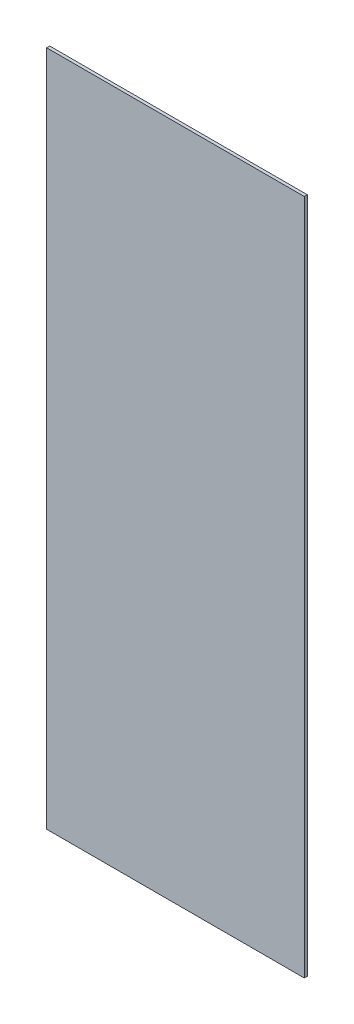
SolidWorks part; units mm, degrees
ref_plane "Front Plane" through (0, 0, 0) normal (0, 0, 1) x (1, 0, 0)
ref_plane "Top Plane" through (0, 0, 0) normal (0, 1, 0) x (1, 0, 0)
ref_plane "Right Plane" through (0, 0, 0) normal (1, 0, 0) x (0, 0, -1)
sketch "Sketch1" plane through (0, 0, 0) normal (0, 0, 1) x (1, 0, 0)
  line L0 (418.175, 166.6) -> (418.175, 165.1) construction
  line L1 (418.175, 165.85) -> (544.425, 165.85)
  line L2 (418.175, 165.85) -> (418.175, -165.85)
  line L3 (418.175, -165.85) -> (544.425, -165.85)
  line L4 (544.425, 165.85) -> (544.425, -165.85)
  line L5 (544.425, -165.1) -> (544.425, -166.6) construction
extrude "Extrude1" add sketch "Sketch1" along normal blind 1.5
